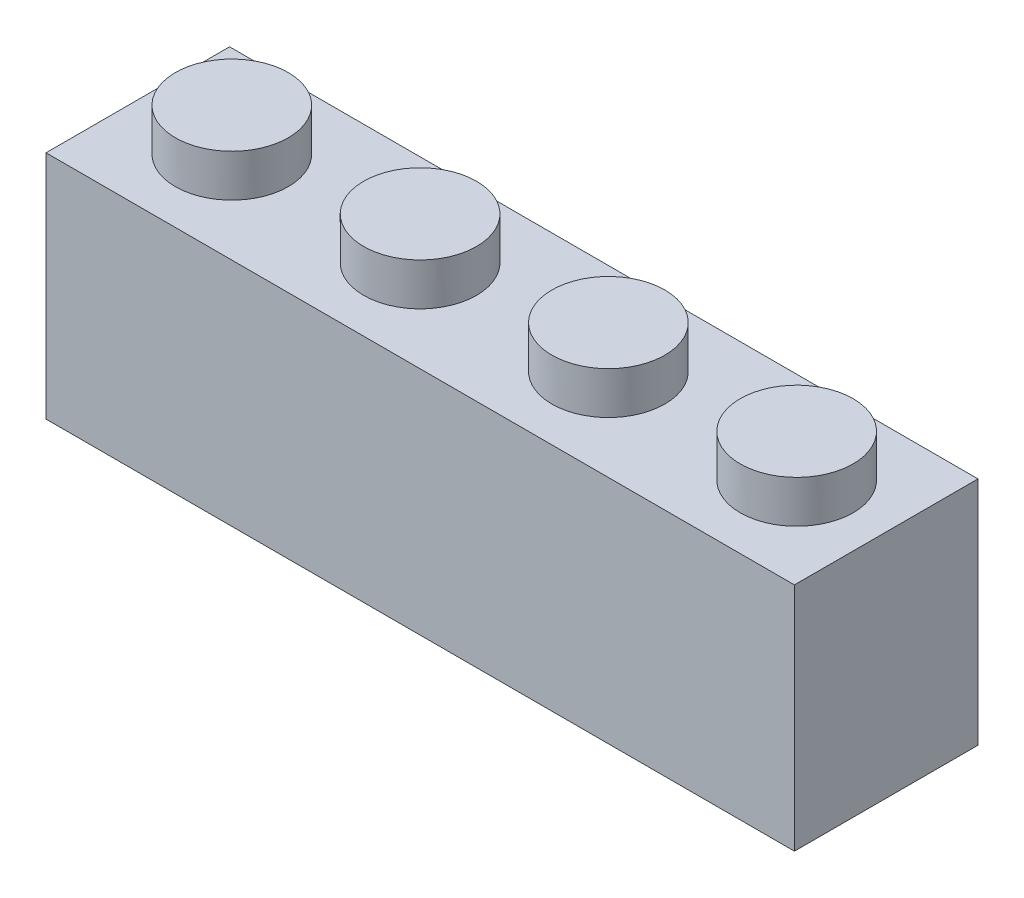
SolidWorks part; units mm, degrees
ref_plane "Front Plane" through (0, 0, 0) normal (0, 0, 1) x (1, 0, 0)
ref_plane "Top Plane" through (0, 0, 0) normal (0, 1, 0) x (1, 0, 0)
ref_plane "Right Plane" through (0, 0, 0) normal (1, 0, 0) x (0, 0, -1)
sketch "Sketch1" plane through (0, 0, 0) normal (0, 1, 0) x (1, 0, 0)
  line L1 (-15.9, 3.9) -> (15.9, 3.9)
  line L2 (-15.9, 3.9) -> (-15.9, -3.9)
  line L3 (-15.9, -3.9) -> (15.9, -3.9)
  line L4 (15.9, 3.9) -> (15.9, -3.9)
  line L5 (-15.9, 3.9) -> (15.9, -3.9) construction
  line L6 (-15.9, -3.9) -> (15.9, 3.9) construction
  point P0 (0, 0)
  dimension "D1" = 31.8
  dimension "D2" = 7.8
extrude "Boss-Extrude1" add sketch "Sketch1" along normal mid plane 9.8
ref_plane "Plane1" through (15.9, 4.9, -3.9) normal (0, -1, 0) x (-1, 0, 0)
sketch "Sketch2" plane through (15.9, 4.9, -3.9) normal (0, -1, 0) x (1, 0, 0)
  circle A0 centre (-27.8048, 3.9) radius 2.4
  circle A1 centre (-19.8048, 3.9) radius 2.4
  circle A2 centre (-11.8048, 3.9) radius 2.4
  circle A3 centre (-3.8048, 3.9) radius 2.4
  dimension "D1" = 4.8
  dimension "D2" = 4
extrude "Boss-Extrude2" add sketch "Sketch2" against normal blind 1.8
sketch "Sketch3" plane through (0, -4.9, 0) normal (0, -1, 0) x (1, 0, 0)
  line L0 (-15.9, -3.9) -> (-15.9, 3.9) construction
  line L1 (-14.3, -2.3) -> (14.3, -2.3)
  line L2 (-14.3, -2.3) -> (-14.3, 2.3)
  line L3 (-14.3, 2.3) -> (14.3, 2.3)
  line L4 (14.3, -2.3) -> (14.3, 2.3)
  line L5 (-14.3, -2.3) -> (14.3, 2.3) construction
  line L6 (-14.3, 2.3) -> (14.3, -2.3) construction
  line L7 (-15.9, 3.9) -> (15.9, 3.9) construction
  point P0 (0, 0)
  dimension "D1" = 1.6
  dimension "D2" = 1.6
extrude "Cut-Extrude1" cut sketch "Sketch3" against normal blind 8
ref_plane "Plane2" through (15.9, 3.3, -3.9) normal (0, -1, 0) x (-1, 0, 0)
sketch "Sketch6" plane through (15.9, 3.3, -3.9) normal (0, -1, 0) x (-1, 0, 0)
  line L0 (0, -7.8) -> (0, 0) construction
  circle A0 centre (7.95, -3.9) radius 1.5
  circle A1 centre (15.9, -3.9) radius 1.5
  circle A2 centre (23.85, -3.9) radius 1.5
  dimension "D2" = 3
  dimension "D1" = 7.95
  dimension "D3" = 3
extrude "Boss-Extrude3" add sketch "Sketch6" along normal blind 8
